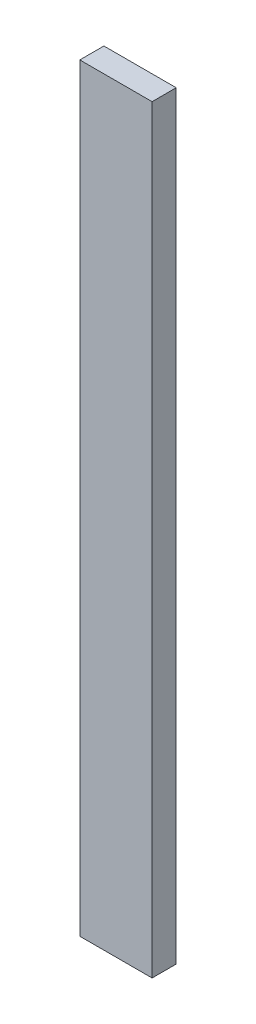
SolidWorks part; units mm, degrees
ref_plane "Front Plane" through (0, 0, 0) normal (0, 0, 1) x (1, 0, 0)
ref_plane "Top Plane" through (0, 0, 0) normal (0, 1, 0) x (1, 0, 0)
ref_plane "Right Plane" through (0, 0, 0) normal (1, 0, 0) x (0, 0, -1)
sketch "Sketch1" plane through (0, 0, 0) normal (0, 1, 0) x (1, 0, 0)
  line L1 (0, 0) -> (38.1, 0)
  line L2 (0, 0) -> (0, 12.7)
  line L3 (0, 12.7) -> (38.1, 12.7)
  line L4 (38.1, 0) -> (38.1, 12.7)
  dimension "D1" = 38.1
  dimension "D2" = 12.7
extrude "Boss-Extrude1" add sketch "Sketch1" along normal blind 400
